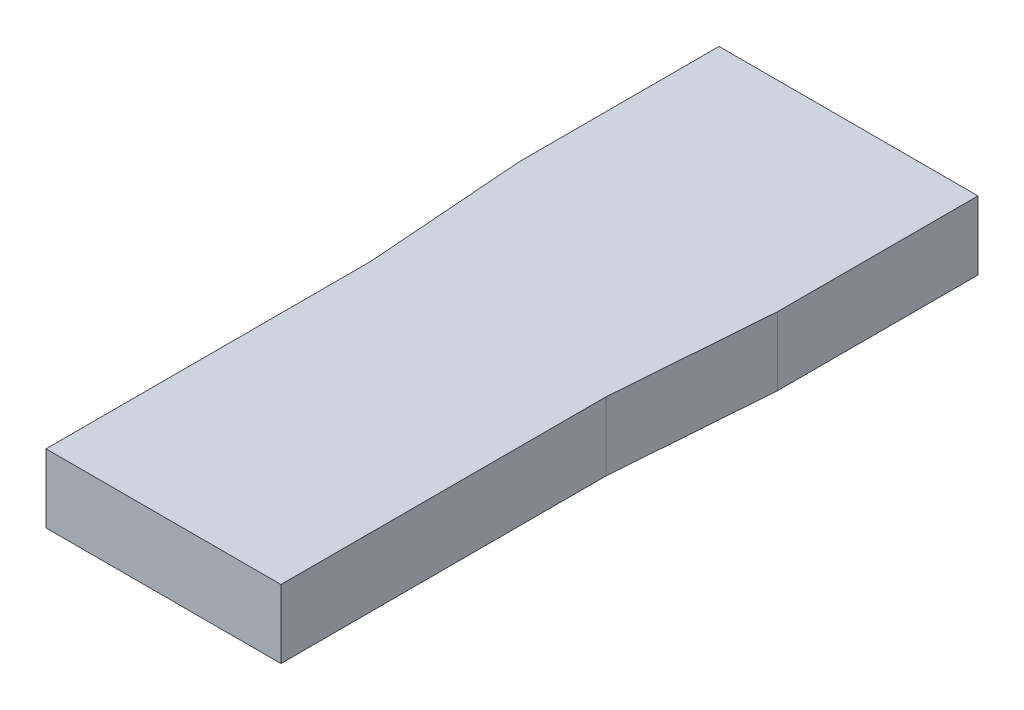
SolidWorks part; units mm, degrees
ref_plane "Front Plane" through (0, 0, 0) normal (0, 0, 1) x (1, 0, 0)
ref_plane "Top Plane" through (0, 0, 0) normal (0, 1, 0) x (1, 0, 0)
ref_plane "Right Plane" through (0, 0, 0) normal (1, 0, 0) x (0, 0, -1)
sketch "Sketch1" plane through (0, 0, 0) normal (0, 1, 0) x (1, 0, 0)
  line L1 (-5.67, -15) -> (5.67, -15)
  line L2 (-5.67, -15) -> (-5.67, 15)
  line L3 (-5.67, 15) -> (5.67, 15)
  line L4 (5.67, -15) -> (5.67, 15)
  line L5 (-5.67, -15) -> (5.67, 15) construction
  line L6 (-5.67, 15) -> (5.67, -15) construction
  point P0 (0, 0)
  dimension "D1" = 11.34
  dimension "D2" = 30
extrude "Boss-Extrude1" add sketch "Sketch1" along normal blind 3
sketch "Sketch2" plane through (0, 3, 0) normal (0, 1, 0) x (1, 0, 0)
  line L0 (-5.145, -15) -> (-5.145, -0.77)
  line L1 (-5.67, -15) -> (5.67, -15) construction
  line L2 (-5.145, -0.77) -> (-5.67, 6.23)
  line L3 (-5.67, 15) -> (-5.67, -15) construction
  line L4 (-5.67, 6.23) -> (-5.67, -15)
  line L5 (-5.67, -15) -> (-5.145, -15)
  line L6 (-5.145, -15) -> (-4.9548, -15.2389)
  dimension "D1" = 8.77
  dimension "D2" = 7
  dimension "D3" = 0.525
extrude "Cut-Extrude1" cut sketch "Sketch2" against normal through all both and the other way through all contours L0 L2 L4 L5
mirror "Mirror1" about plane through (0, 0, 0) normal (1, 0, 0) of "Cut-Extrude1"
